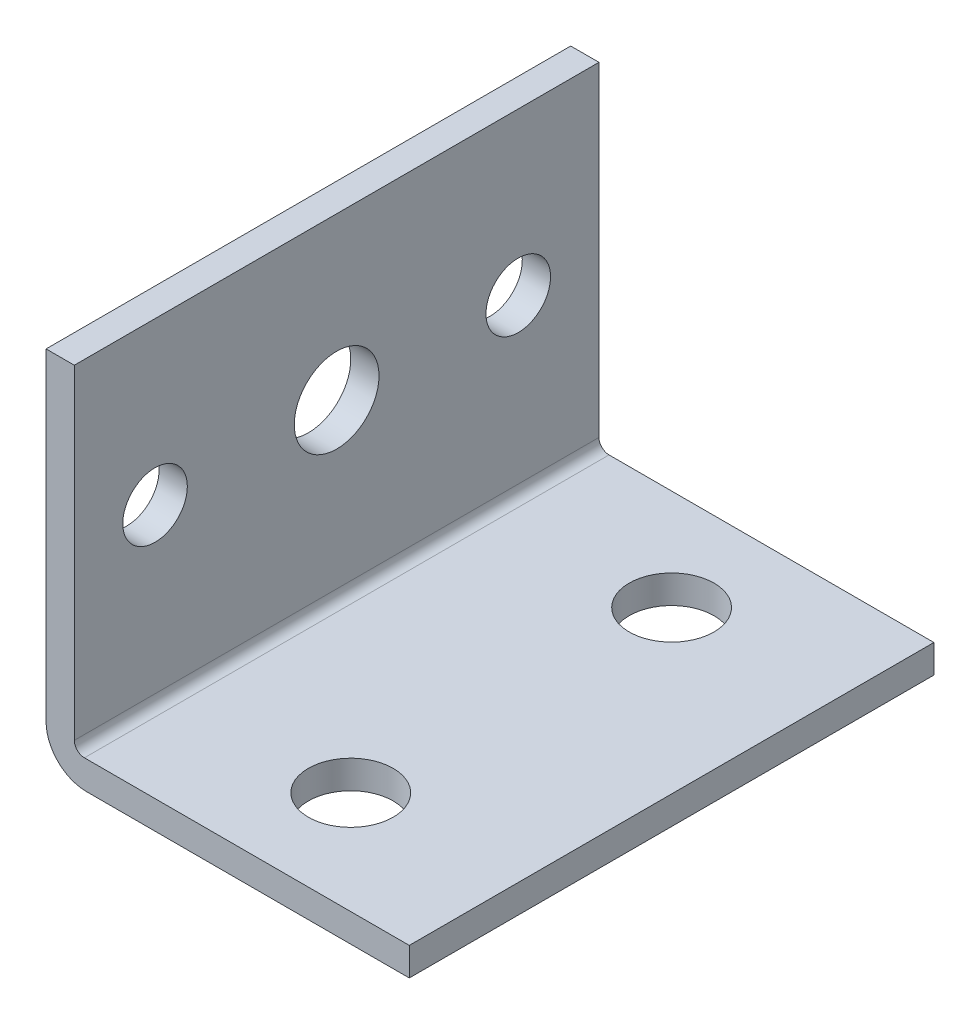
SolidWorks part; units mm, degrees
ref_plane "Front Plane" through (0, 0, 0) normal (0, 0, 1) x (1, 0, 0)
ref_plane "Top Plane" through (0, 0, 0) normal (0, 1, 0) x (1, 0, 0)
ref_plane "Right Plane" through (0, 0, 0) normal (1, 0, 0) x (0, 0, -1)
sketch "Sketch1" plane through (0, 0, 0) normal (0, 0, 1) x (1, 0, 0)
  line L0 (-20.6342, 26.4531) -> (-20.6342, -19.2669)
  line L1 (-20.6342, -19.2669) -> (25.0858, -19.2669)
  line L2 (25.0858, -19.2669) -> (25.0858, -15.7109)
  line L3 (-20.6342, 26.4531) -> (-17.0782, 26.4531)
  line L4 (-17.0782, -15.7109) -> (-17.0782, 26.4531)
  line L5 (-17.0782, -15.7109) -> (25.0858, -15.7109)
  line L6 (25.0858, -15.7109) -> (24.797, -15.8594)
extrude "Boss-Extrude1" add sketch "Sketch1" against normal blind 66.04
fillet "Fillet1" radius 1.27 1 edges at (-17.0782, -15.7109, -33.02)
fillet "Fillet3" radius 5.08 1 edges at (-20.6342, -19.2669, -33.02)
sketch "Sketch2" plane through (-20.6342, 0, 0) normal (-1, 0, 0) x (0, 0, 1)
  circle A0 centre (-33.02, 6.1331) radius 5.334
  circle A1 centre (-55.88, 6.1331) radius 4.064
  circle A2 centre (-10.16, 6.1331) radius 4.064
extrude "Cut-Extrude1" cut sketch "Sketch2" against normal blind 66.04
sketch "Sketch3" plane through (0, -19.2669, 0) normal (0, -1, 0) x (-1, 0, 0)
  circle A0 centre (-4.7658, 12.954) radius 5.334
  circle A1 centre (-4.7658, 53.34) radius 5.334
extrude "Cut-Extrude2" cut sketch "Sketch3" against normal blind 66.04
